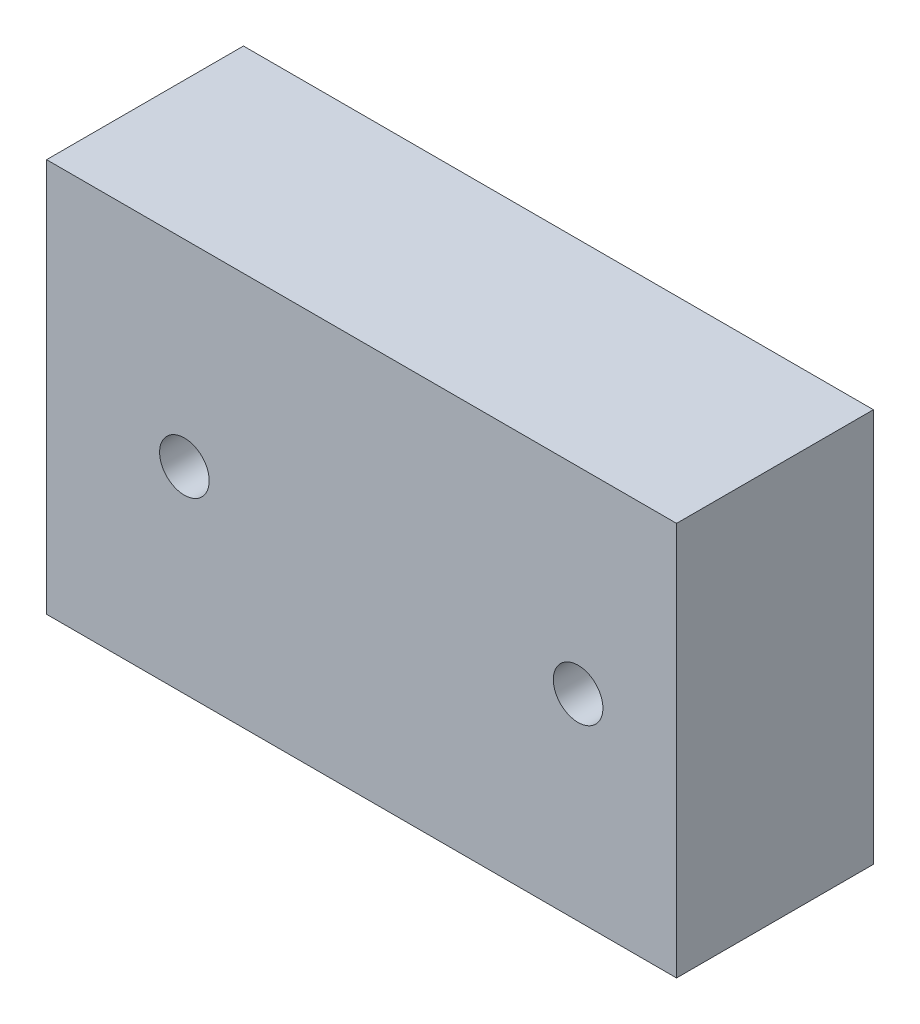
SolidWorks part; units mm, degrees
ref_plane "Front Plane" through (0, 0, 0) normal (0, 0, 1) x (1, 0, 0)
ref_plane "Top Plane" through (0, 0, 0) normal (0, 1, 0) x (1, 0, 0)
ref_plane "Right Plane" through (0, 0, 0) normal (1, 0, 0) x (0, 0, -1)
sketch "Sketch1" plane through (0, 0, 0) normal (0, 0, 1) x (1, 0, 0)
  line L1 (0, 0) -> (20.32, 0)
  line L2 (0, 0) -> (0, 12.7)
  line L3 (0, 12.7) -> (20.32, 12.7)
  line L4 (20.32, 0) -> (20.32, 12.7)
  dimension "D1" = 12.7
  dimension "D2" = 20.32
extrude "Boss-Extrude1" add sketch "Sketch1" along normal blind 6.35
hole_wizard "M2x0.4 Tapped Hole1" positions "Sketch4" profile "Sketch3" tap size "M2x0.4" standard "ANSI Metric" end condition through all
sketch "Sketch4" plane through (0, 0, 6.35) normal (0, 0, 1) x (1, 0, 0)
  line L0 (4.445, 12.7) -> (4.445, 0) construction
  line L1 (20.32, 12.7) -> (0, 12.7) construction
  line L2 (0, 0) -> (20.32, 0) construction
  line L4 (17.145, 12.7) -> (17.145, 0) construction
  line L8 (20.32, 0) -> (20.32, 12.7) construction
  point P24 (4.445, 6.35)
  point P26 (17.145, 6.35)
  dimension "D1" = 3.175
  dimension "D2" = 12.7
  dimension "D3" = 6.35
  dimension "D4" = 6.35
sketch "Sketch3" plane through (17.145, 6.35, 6.35) normal (1, 0, 0) x (0, -1, 0)
  line L0 (0, 0) -> (0, 6.35)
  line L1 (0, 6.35) -> (0.8, 6.35)
  line L2 (0.8, 6.35) -> (0.8, 0)
  line L5 (0.8, 0) -> (0, 0)
  line L11 (0, -6.35) -> (0, 107.95) construction
  dimension "Thru Tap Drill Dia." = 1.6
  dimension "Thru Tap Drill Depth" = 6.35
cosmetic thread "Hole Thread1"
cosmetic thread "Hole Thread2"
